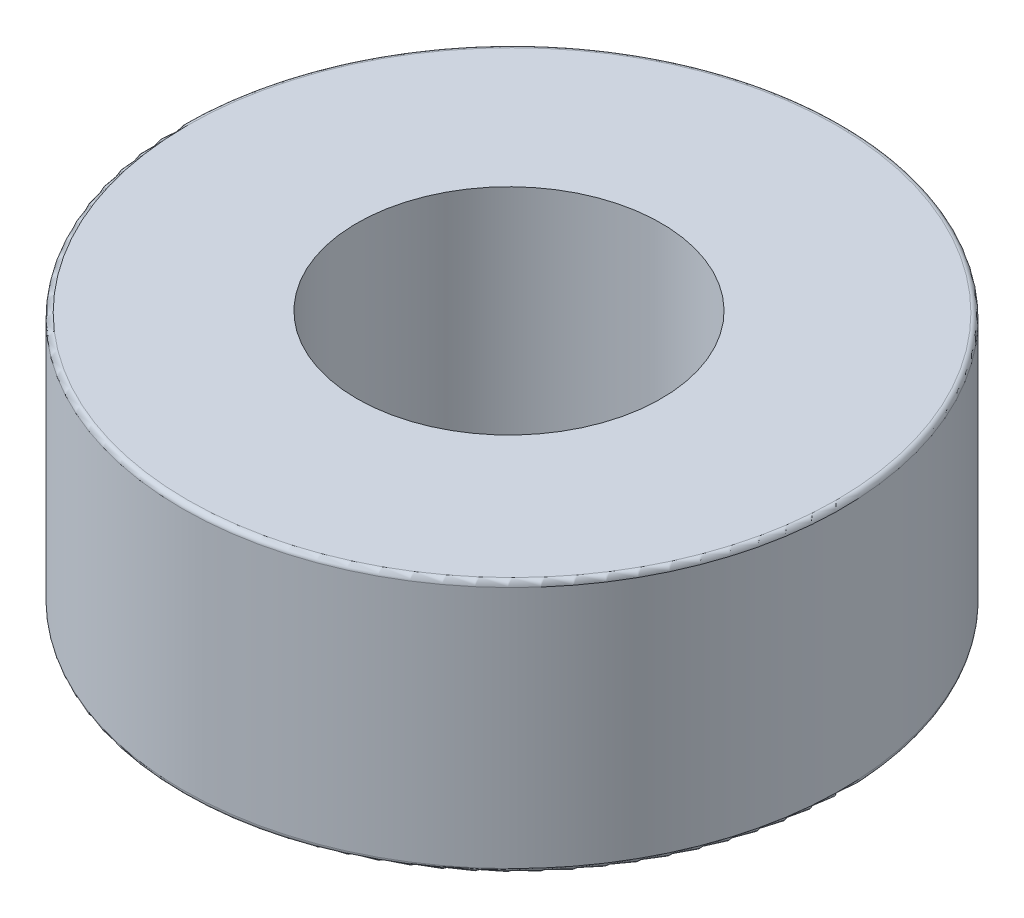
SolidWorks part; units mm, degrees
material "Stainless Steel (ferritic)"
ref_plane "Front Plane" through (0, 0, 0) normal (0, 0, 1) x (1, 0, 0)
ref_plane "Top Plane" through (0, 0, 0) normal (0, 1, 0) x (1, 0, 0)
ref_plane "Right Plane" through (0, 0, 0) normal (1, 0, 0) x (0, 0, -1)
sketch "Sketch1" plane through (0, 0, 0) normal (0, 1, 0) x (1, 0, 0)
  circle A0 centre (0, 0) radius 3
  circle A1 centre (0.0598, 0) radius 6.5
  dimension "D1" = 6
  dimension "D2" = 13
extrude "Boss-Extrude1" add sketch "Sketch1" along normal blind 5
fillet "Fillet1" radius 0.1 2 edges at (0.0598, 0, 6.5) (0.0598, 5, 6.5)
